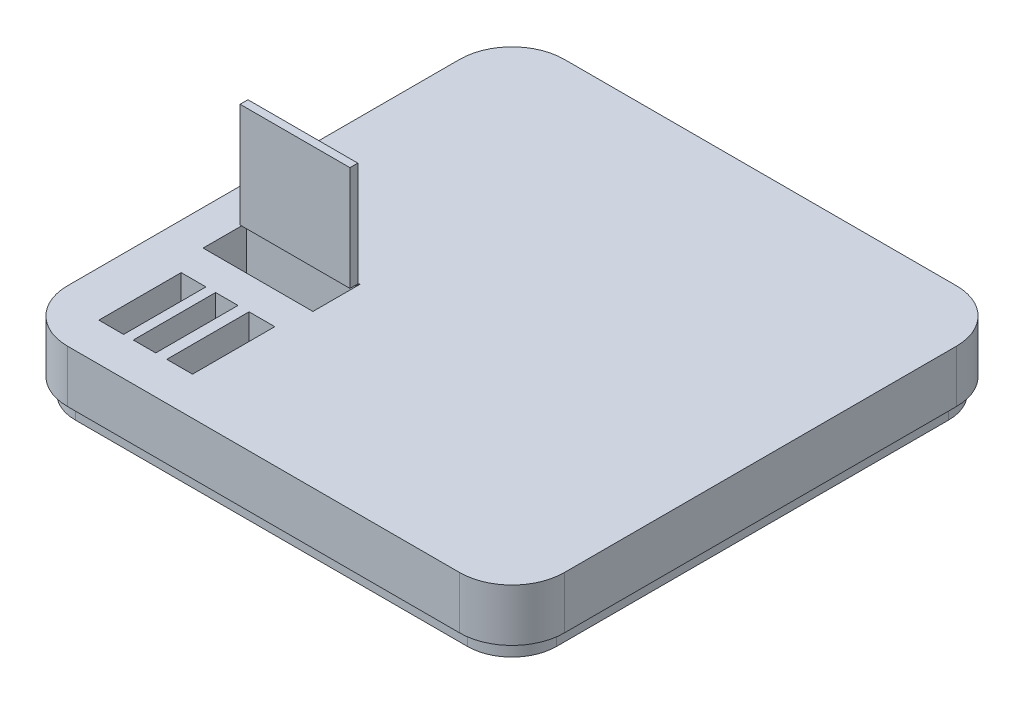
SolidWorks part; units mm, degrees
ref_plane "Front Plane" through (0, 0, 0) normal (0, 0, 1) x (1, 0, 0)
ref_plane "Top Plane" through (0, 0, 0) normal (0, 1, 0) x (1, 0, 0)
ref_plane "Right Plane" through (0, 0, 0) normal (1, 0, 0) x (0, 0, -1)
sketch "Sketch1" plane through (-45.2428, 0, -5.5986) normal (0, 1, 0) x (1, 0, 0)
  line L1 (-47.5, 47.5) -> (47.5, 47.5)
  line L2 (-47.5, 47.5) -> (-47.5, -47.5)
  line L3 (-47.5, -47.5) -> (47.5, -47.5)
  line L4 (47.5, 47.5) -> (47.5, -47.5)
  line L5 (-47.5, 47.5) -> (47.5, -47.5) construction
  line L6 (-47.5, -47.5) -> (47.5, 47.5) construction
  point P0 (0, 0)
  dimension "D1" = 95
  dimension "D2" = 95
extrude "Boss-Extrude1" add sketch "Sketch1" along normal blind 10
fillet "Fillet1" radius 10 4 edges at (-92.7428, 5, -53.0986) (-92.7428, 5, 41.9014) (2.2572, 5, -53.0986) (2.2572, 5, 41.9014)
sketch "Sketch4" plane through (-45.2428, 0, -5.5986) normal (0, -1, 0) x (1, 0, 0)
  line L9 (-46, 37.5) -> (-46, -37.5)
  line L10 (-37.5, -46) -> (37.5, -46)
  line L11 (46, -37.5) -> (46, 37.5)
  line L12 (37.5, 46) -> (-37.5, 46)
  line L13 (-46, 37.5) -> (-46, -37.5)
  line L14 (-37.5, -46) -> (37.5, -46)
  line L15 (46, -37.5) -> (46, 37.5)
  line L16 (37.5, 46) -> (-37.5, 46)
  arc A8 (-46, -37.5) -> (-37.5, -46) centre (-37.5, -37.5) ccw
  arc A9 (37.5, -46) -> (46, -37.5) centre (37.5, -37.5) ccw
  arc A10 (46, 37.5) -> (37.5, 46) centre (37.5, 37.5) ccw
  arc A11 (-37.5, 46) -> (-46, 37.5) centre (-37.5, 37.5) ccw
  arc A12 (-46, -37.5) -> (-37.5, -46) centre (-37.5, -37.5) ccw
  arc A13 (37.5, -46) -> (46, -37.5) centre (37.5, -37.5) ccw
  arc A14 (46, 37.5) -> (37.5, 46) centre (37.5, 37.5) ccw
  arc A15 (-37.5, 46) -> (-46, 37.5) centre (-37.5, 37.5) ccw
  dimension "D1" = 1.5
extrude "Boss-Extrude2" add sketch "Sketch4" along normal blind 3
sketch "Sketch5" plane through (-45.2428, 10, -5.5986) normal (0, 1, 0) x (1, 0, 0)
  line L1 (-38.8123, -40.1968) -> (-34.0788, -40.1968)
  line L2 (-38.8123, -40.1968) -> (-38.8123, -24.4571)
  line L3 (-38.8123, -24.4571) -> (-34.0788, -24.4571)
  line L4 (-34.0788, -40.1968) -> (-34.0788, -24.4571)
  line L5 (-38.8123, -40.1968) -> (-34.0788, -24.4571) construction
  line L6 (-38.8123, -24.4571) -> (-34.0788, -40.1968) construction
  line L7 (-32.2251, -40.1968) -> (-27.9392, -40.1968)
  line L8 (-32.2251, -40.1968) -> (-32.2251, -24.4571)
  line L9 (-32.2251, -24.4571) -> (-27.9392, -24.4571)
  line L10 (-27.9392, -40.1968) -> (-27.9392, -24.4571)
  line L11 (-32.2251, -40.1968) -> (-27.9392, -24.4571) construction
  line L12 (-32.2251, -24.4571) -> (-27.9392, -40.1968) construction
  line L13 (-25.8271, -40.1968) -> (-20.9046, -40.1968)
  line L14 (-25.8271, -40.1968) -> (-25.8271, -24.4571)
  line L15 (-25.8271, -24.4571) -> (-20.9046, -24.4571)
  line L16 (-20.9046, -40.1968) -> (-20.9046, -24.4571)
  line L17 (-25.8271, -40.1968) -> (-20.9046, -24.4571) construction
  line L18 (-25.8271, -24.4571) -> (-20.9046, -40.1968) construction
  point P0 (-36.4455, -32.3269)
  point P5 (-30.0822, -32.3269)
  point P10 (-23.3658, -32.3269)
extrude "Cut-Extrude1" cut sketch "Sketch5" against normal blind 10
sketch "Sketch10" plane through (0, 10, 0) normal (0, 1, 0) x (1, 0, 0)
  text T0 "   i - Voke Drowsiness Detector"
  point P1 (0, 0)
sketch "Sketch14" plane through (0, 10, 0) normal (0, 1, 0) x (1, 0, 0)
  line L1 (-86.0219, -3.6928) -> (-65.0219, -3.6928)
  line L2 (-86.0219, -3.6928) -> (-86.0219, -12.6928)
  line L3 (-86.0219, -12.6928) -> (-65.0219, -12.6928)
  line L4 (-65.0219, -3.6928) -> (-65.0219, -12.6928)
  line L5 (-86.0219, -3.6928) -> (-65.0219, -12.6928) construction
  line L6 (-86.0219, -12.6928) -> (-65.0219, -3.6928) construction
  point P0 (-75.5219, -8.1928)
  point P5 (0, 0)
  point P6 (0, 0)
extrude "Cut-Extrude2" cut sketch "Sketch14" against normal blind 10
sketch "Sketch16" plane through (0, 0, 0) normal (0, 1, 0) x (1, 0, 0)
  line L1 (-86.5278, -4.3884) -> (-65.1918, -4.3884)
  line L2 (-86.5278, -4.3884) -> (-86.5278, 9.2303)
  line L3 (-86.5278, 9.2303) -> (-65.1918, 9.2303)
  line L4 (-65.1918, -4.3884) -> (-65.1918, 9.2303)
  line L5 (-86.5278, -4.3884) -> (-65.1918, 9.2303) construction
  line L6 (-86.5278, 9.2303) -> (-65.1918, -4.3884) construction
  point P0 (-75.8598, 2.4209)
extrude "Boss-Extrude7" add sketch "Sketch16" along normal blind 10
sketch "Sketch20" plane through (0, 10, 0) normal (0, 1, 0) x (1, 0, 0)
  line L1 (-86.3008, -5.337) -> (-65.3008, -5.337)
  line L2 (-86.3008, -5.337) -> (-86.3008, -3.837)
  line L3 (-86.3008, -3.837) -> (-65.3008, -3.837)
  line L4 (-65.3008, -5.337) -> (-65.3008, -3.837)
  line L5 (-86.3008, -5.337) -> (-65.3008, -3.837) construction
  line L6 (-86.3008, -3.837) -> (-65.3008, -5.337) construction
  point P0 (-75.8008, -4.587)
extrude "Boss-Extrude13" add sketch "Sketch20" along normal blind 20
